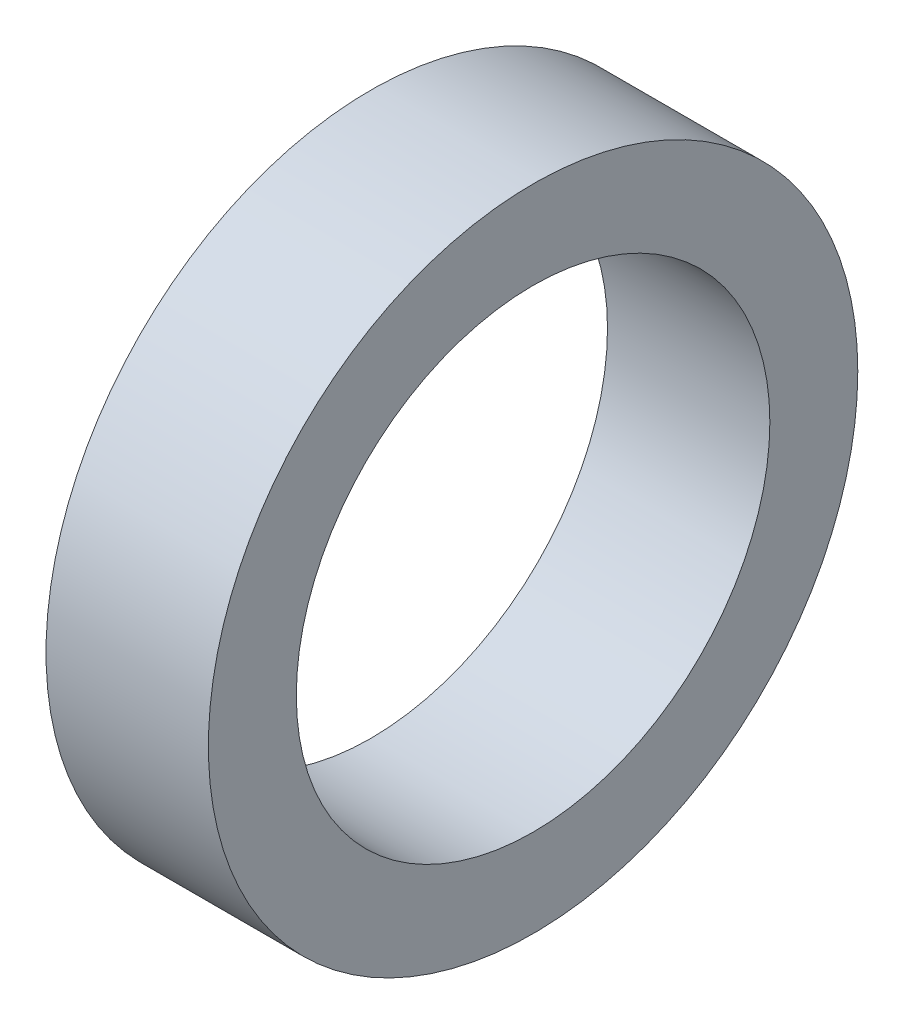
SolidWorks part; units mm, degrees
ref_plane "前视基准面" through (0, 0, 0) normal (0, 0, 1) x (1, 0, 0)
ref_plane "上视基准面" through (0, 0, 0) normal (0, 1, 0) x (1, 0, 0)
ref_plane "右视基准面" through (0, 0, 0) normal (1, 0, 0) x (0, 0, -1)
other "Configuration Table"
sketch "草图1" plane through (0, 0, 0) normal (1, 0, 0) x (0, 0, -1)
  circle A0 centre (0, 0) radius 8.75
  circle A1 centre (0, 0) radius 12
  dimension "D1" = 17.5
  dimension "D2" = 24
extrude "凸台-拉伸1" add sketch "草图1" along normal blind 6
